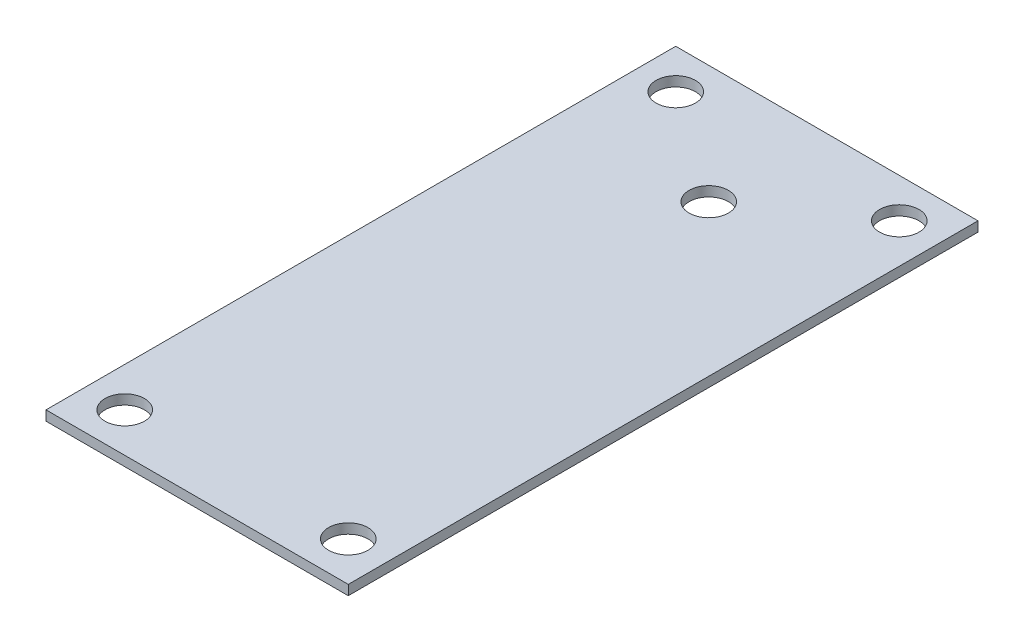
SolidWorks part; units mm, degrees
ref_plane "Front Plane" through (0, 0, 0) normal (0, 0, 1) x (1, 0, 0)
ref_plane "Top Plane" through (0, 0, 0) normal (0, 1, 0) x (1, 0, 0)
ref_plane "Right Plane" through (0, 0, 0) normal (1, 0, 0) x (0, 0, -1)
sketch "Sketch1" plane through (0, 0, 0) normal (0, 1, 0) x (1, 0, 0)
  line L0 (-18.034, 44.45) -> (-18.034, -44.45) construction
  line L1 (-24.384, 50.8) -> (24.384, 50.8)
  line L2 (-24.384, 50.8) -> (-24.384, -50.8)
  line L3 (-24.384, -50.8) -> (24.384, -50.8)
  line L4 (24.384, 50.8) -> (24.384, -50.8)
  line L5 (-14.605, 50.8) -> (14.605, 50.8) construction
  line L6 (-14.605, 50.8) -> (-14.605, -50.8) construction
  line L7 (-14.605, -50.8) -> (14.605, -50.8) construction
  line L8 (14.605, 50.8) -> (14.605, -50.8) construction
  line L9 (-18.034, 44.45) -> (18.034, 44.45) construction
  circle A0 centre (-18.034, 44.45) radius 3.175
  circle A1 centre (18.034, 44.45) radius 3.175
  circle A2 centre (18.034, -44.45) radius 3.175
  circle A3 centre (-18.034, -44.45) radius 3.175
  point P8 (0, 50.8)
  point P9 (0, -50.8)
  point P10 (24.384, 0)
  point P20 (-18.034, 0)
  point P21 (0, 44.45)
  point P24 (-19.05, 44.45)
  point P25 (19.05, 44.45)
  dimension "D4" = 6.35
  dimension "D1" = 101.6
  dimension "D2" = 29.718
  dimension "D3" = 29.21
  dimension "D5" = 6.35
  dimension "D6" = 6.35
extrude "Boss-Extrude1" add sketch "Sketch1" along normal blind 1.5875
sketch "Sketch2" plane through (0, 1.5875, 0) normal (0, 1, 0) x (1, 0, 0)
  line L0 (24.384, 50.8) -> (-24.384, 50.8) construction
  circle A0 centre (0, 31.75) radius 3.175
  point P2 (0, 0)
  dimension "D1" = 6.35
  dimension "D2" = 19.05
extrude "Cut-Extrude1" cut sketch "Sketch2" against normal up to next
